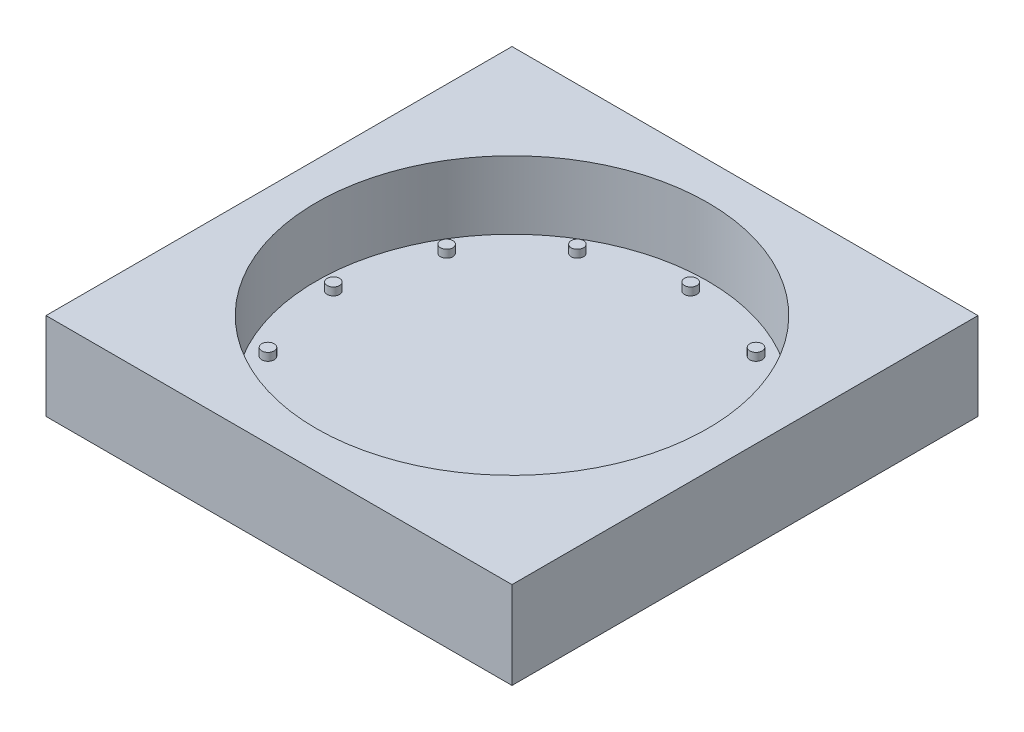
SolidWorks part; units mm, degrees
ref_plane "Front Plane" through (0, 0, 0) normal (0, 0, 1) x (1, 0, 0)
ref_plane "Top Plane" through (0, 0, 0) normal (0, 1, 0) x (1, 0, 0)
ref_plane "Right Plane" through (0, 0, 0) normal (1, 0, 0) x (0, 0, -1)
sketch "Sketch1" plane through (0, 0, 0) normal (0, 1, 0) x (1, 0, 0)
  line L1 (-76.2, -76.2) -> (76.2, -76.2)
  line L2 (-76.2, -76.2) -> (-76.2, 76.2)
  line L3 (-76.2, 76.2) -> (76.2, 76.2)
  line L4 (76.2, -76.2) -> (76.2, 76.2)
  line L5 (-76.2, -76.2) -> (76.2, 76.2) construction
  line L6 (-76.2, 76.2) -> (76.2, -76.2) construction
  circle A0 centre (0, 0) radius 64.008
  dimension "D1" = 128.016
  dimension "D2" = 152.4
  dimension "D3" = 152.4
extrude "Boss-Extrude1" add sketch "Sketch1" along normal blind 22.225
sketch "Sketch2" plane through (0, 0, 0) normal (0, -1, 0) x (-1, 0, 0)
  line L1 (76.2, -76.2) -> (-76.2, -76.2)
  line L2 (76.2, -76.2) -> (76.2, 76.2)
  line L3 (76.2, 76.2) -> (-76.2, 76.2)
  line L4 (-76.2, -76.2) -> (-76.2, 76.2)
extrude "Boss-Extrude2" add sketch "Sketch2" along normal blind 6.35
sketch "Sketch3" plane through (0, 0, 0) normal (0, 1, 0) x (1, 0, 0)
  circle A1 centre (-58.42, 0) radius 2.032
  dimension "D2" = 4.064
  dimension "D1" = 58.42
extrude "Boss-Extrude3" add sketch "Sketch3" along normal blind 2.54
pattern_circular "CirPattern1" count 12 over 360 about axis through (0, 0, 0) along (0, 1, 0) of "Boss-Extrude3"
